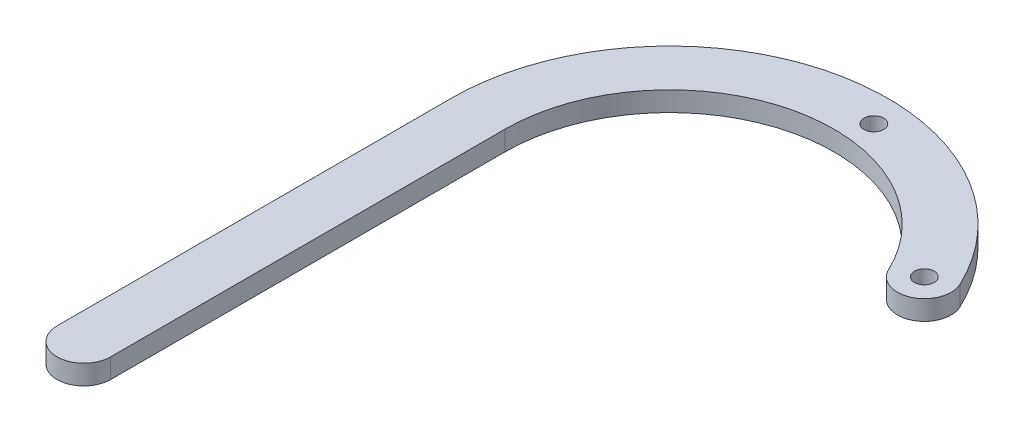
SolidWorks part; units mm, degrees
ref_plane "Front" through (0, 0, 0) normal (0, 0, 1) x (1, 0, 0)
ref_plane "Top" through (0, 0, 0) normal (0, 1, 0) x (1, 0, 0)
ref_plane "Right" through (0, 0, 0) normal (1, 0, 0) x (0, 0, -1)
sketch "Sketch2" plane through (0, 0, 0) normal (0, 1, 0) x (1, 0, 0)
  line L0 (-64.4336, -10.72) -> (-64.4336, -74.22)
  line L1 (-55.7976, -10.72) -> (-55.7976, -74.22)
  arc A0 (0, 0) -> (-52.9784, 9.5967) centre (-29.3002, -10.72) ccw construction
  arc A1 (2.4621, 4.2966) -> (-64.4336, -10.72) centre (-29.3002, -10.72) ccw
  arc A2 (-5.3453, 0.6054) -> (-55.7976, -10.72) centre (-29.3002, -10.72) ccw
  arc A4 (2.4621, 4.2966) -> (-5.3453, 0.6054) centre (-1.4416, 2.451) cw
  arc A5 (-55.7976, -74.22) -> (-64.4336, -74.22) centre (-60.1156, -74.22) cw
  point P3 (-39.6898, 16.6937)
  point P7 (-29.3002, 20.4797)
  point P8 (0, 0)
  point P9 (0, 0)
  dimension "D1" = 35.1333
  dimension "D3" = 26.4973
  dimension "D4" = 31.1997
  dimension "D5" = 54.356
  dimension "D6" = 83.8167
  dimension "D2" = 63.5
extrude "Boss-Extrude1" add sketch "Sketch2" along normal blind 3.175
sketch "Sketch5" plane through (0, 3.175, 0) normal (0, 1, 0) x (1, 0, 0)
  circle A0 centre (-26.8416, 19.723) radius 1.5875
  circle A1 centre (-1.4416, 2.451) radius 1.5875
  dimension "D1" = 3.175
  dimension "D2" = 3.175
  dimension "D3" = 17.272
  dimension "D4" = 25.4
extrude "Cut-Extrude1" cut sketch "Sketch5" against normal through all
